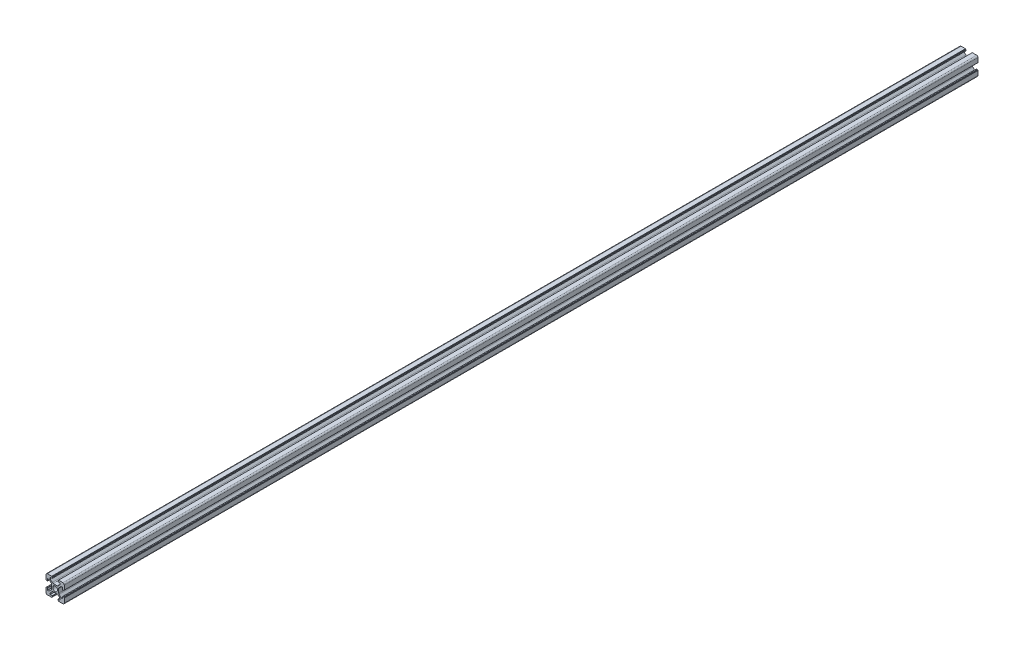
SolidWorks part; units mm, degrees
material "6063 T5"
ref_plane "Спереди" through (0, 0, 0) normal (0, 0, 1) x (1, 0, 0)
ref_plane "Сверху" through (0, 0, 0) normal (0, 1, 0) x (1, 0, 0)
ref_plane "Справа" through (0, 0, 0) normal (1, 0, 0) x (0, 0, -1)
sketch "Эскиз3" plane through (0, 0, 0) normal (0, 0, 1) x (1, 0, 0)
  line L0 (-10, 5.5) -> (-10, 8.5)
  line L5 (-8.5, 10) -> (-5.5, 10)
  line L7 (-9.9529, 9.1691) -> (10.0471, 9.1691) construction
  line L8 (5.5, 10) -> (8.5, 10)
  line L9 (10, 8.5) -> (10, 5.5)
  line L10 (10, -5.5) -> (10, -8.5)
  line L11 (8.5, -10) -> (5.5, -10)
  line L12 (-5.5, -10) -> (-8.5, -10)
  line L19 (-10, -8.5) -> (-10, -5.5)
  circle A0 centre (0, 0) radius 2.6
  arc A1 (-8.5, -10) -> (-10, -8.5) centre (-8.5, -8.5) cw
  arc A2 (10, -8.5) -> (8.5, -10) centre (8.5, -8.5) cw
  arc A3 (8.5, 10) -> (10, 8.5) centre (8.5, 8.5) cw
  arc A4 (-10, 8.5) -> (-8.5, 10) centre (-8.5, 8.5) cw
  point P0 (0, 0)
  point P4 (0, 0)
  point P30 (0, 0)
  line B0 (-8.2, 5.5) -> (-6.6, 5.5)
  line B1 (-6.6, 5.5) -> (-4.3393, 3.2393)
  line B2 (-3.9, 2.1787) -> (-3.9, -2.1787)
  line B3 (-4.3393, -3.2393) -> (-6.6, -5.5)
  line B4 (-6.6, -5.5) -> (-8.2, -5.5)
  line B5 (-8.2, -5.5) -> (-8.2, -3.25)
  line B6 (-8.35, -3.1) -> (-9.35, -3.1)
  line B7 (-9.5, -3.25) -> (-9.5, -3.45)
  line B8 (-9.65, -3.6) -> (-9.85, -3.6)
  line B9 (-9.85, 3.6) -> (-9.65, 3.6)
  line B10 (-9.5, 3.45) -> (-9.5, 3.25)
  line B11 (-9.35, 3.1) -> (-8.35, 3.1)
  line B12 (-8.2, 3.25) -> (-8.2, 5.5)
  line B13 (-10, 3.75) -> (-10, 5.5)
  line B14 (-10, -3.75) -> (-10, -5.5)
  line B15 (-10, 5.5) -> (-10, -5.5) construction
  arc B16 (-8.2, -3.25) -> (-8.35, -3.1) centre (-8.35, -3.25) ccw
  arc B17 (-9.35, -3.1) -> (-9.5, -3.25) centre (-9.35, -3.25) ccw
  arc B18 (-9.5, -3.45) -> (-9.65, -3.6) centre (-9.65, -3.45) cw
  arc B19 (-9.85, -3.6) -> (-10, -3.75) centre (-9.85, -3.75) ccw
  arc B20 (-8.35, 3.1) -> (-8.2, 3.25) centre (-8.35, 3.25) ccw
  arc B21 (-9.5, 3.25) -> (-9.35, 3.1) centre (-9.35, 3.25) ccw
  arc B22 (-9.65, 3.6) -> (-9.5, 3.45) centre (-9.65, 3.45) cw
  arc B23 (-10, 3.75) -> (-9.85, 3.6) centre (-9.85, 3.75) ccw
  arc B24 (-3.9, -2.1787) -> (-4.3393, -3.2393) centre (-5.4, -2.1787) cw
  arc B25 (-4.3393, 3.2393) -> (-3.9, 2.1787) centre (-5.4, 2.1787) cw
  line B26 (5.5, 8.2) -> (5.5, 6.6)
  line B27 (5.5, 6.6) -> (3.2393, 4.3393)
  line B28 (2.1787, 3.9) -> (-2.1787, 3.9)
  line B29 (-3.2393, 4.3393) -> (-5.5, 6.6)
  line B30 (-5.5, 6.6) -> (-5.5, 8.2)
  line B31 (-5.5, 8.2) -> (-3.25, 8.2)
  line B32 (-3.1, 8.35) -> (-3.1, 9.35)
  line B33 (-3.25, 9.5) -> (-3.45, 9.5)
  line B34 (-3.6, 9.65) -> (-3.6, 9.85)
  line B35 (3.6, 9.85) -> (3.6, 9.65)
  line B36 (3.45, 9.5) -> (3.25, 9.5)
  line B37 (3.1, 9.35) -> (3.1, 8.35)
  line B38 (3.25, 8.2) -> (5.5, 8.2)
  line B39 (3.75, 10) -> (5.5, 10)
  line B40 (-3.75, 10) -> (-5.5, 10)
  line B41 (5.5, 10) -> (-5.5, 10) construction
  arc B42 (-3.25, 8.2) -> (-3.1, 8.35) centre (-3.25, 8.35) ccw
  arc B43 (-3.1, 9.35) -> (-3.25, 9.5) centre (-3.25, 9.35) ccw
  arc B44 (-3.45, 9.5) -> (-3.6, 9.65) centre (-3.45, 9.65) cw
  arc B45 (-3.6, 9.85) -> (-3.75, 10) centre (-3.75, 9.85) ccw
  arc B46 (3.1, 8.35) -> (3.25, 8.2) centre (3.25, 8.35) ccw
  arc B47 (3.25, 9.5) -> (3.1, 9.35) centre (3.25, 9.35) ccw
  arc B48 (3.6, 9.65) -> (3.45, 9.5) centre (3.45, 9.65) cw
  arc B49 (3.75, 10) -> (3.6, 9.85) centre (3.75, 9.85) ccw
  arc B50 (-2.1787, 3.9) -> (-3.2393, 4.3393) centre (-2.1787, 5.4) cw
  arc B51 (3.2393, 4.3393) -> (2.1787, 3.9) centre (2.1787, 5.4) cw
  line B52 (8.2, -5.5) -> (6.6, -5.5)
  line B53 (6.6, -5.5) -> (4.3393, -3.2393)
  line B54 (3.9, -2.1787) -> (3.9, 2.1787)
  line B55 (4.3393, 3.2393) -> (6.6, 5.5)
  line B56 (6.6, 5.5) -> (8.2, 5.5)
  line B57 (8.2, 5.5) -> (8.2, 3.25)
  line B58 (8.35, 3.1) -> (9.35, 3.1)
  line B59 (9.5, 3.25) -> (9.5, 3.45)
  line B60 (9.65, 3.6) -> (9.85, 3.6)
  line B61 (9.85, -3.6) -> (9.65, -3.6)
  line B62 (9.5, -3.45) -> (9.5, -3.25)
  line B63 (9.35, -3.1) -> (8.35, -3.1)
  line B64 (8.2, -3.25) -> (8.2, -5.5)
  line B65 (10, -3.75) -> (10, -5.5)
  line B66 (10, 3.75) -> (10, 5.5)
  line B67 (10, -5.5) -> (10, 5.5) construction
  arc B68 (8.2, 3.25) -> (8.35, 3.1) centre (8.35, 3.25) ccw
  arc B69 (9.35, 3.1) -> (9.5, 3.25) centre (9.35, 3.25) ccw
  arc B70 (9.5, 3.45) -> (9.65, 3.6) centre (9.65, 3.45) cw
  arc B71 (9.85, 3.6) -> (10, 3.75) centre (9.85, 3.75) ccw
  arc B72 (8.35, -3.1) -> (8.2, -3.25) centre (8.35, -3.25) ccw
  arc B73 (9.5, -3.25) -> (9.35, -3.1) centre (9.35, -3.25) ccw
  arc B74 (9.65, -3.6) -> (9.5, -3.45) centre (9.65, -3.45) cw
  arc B75 (10, -3.75) -> (9.85, -3.6) centre (9.85, -3.75) ccw
  arc B76 (3.9, 2.1787) -> (4.3393, 3.2393) centre (5.4, 2.1787) cw
  arc B77 (4.3393, -3.2393) -> (3.9, -2.1787) centre (5.4, -2.1787) cw
  line B78 (-5.5, -8.2) -> (-5.5, -6.6)
  line B79 (-5.5, -6.6) -> (-3.2393, -4.3393)
  line B80 (-2.1787, -3.9) -> (2.1787, -3.9)
  line B81 (3.2393, -4.3393) -> (5.5, -6.6)
  line B82 (5.5, -6.6) -> (5.5, -8.2)
  line B83 (5.5, -8.2) -> (3.25, -8.2)
  line B84 (3.1, -8.35) -> (3.1, -9.35)
  line B85 (3.25, -9.5) -> (3.45, -9.5)
  line B86 (3.6, -9.65) -> (3.6, -9.85)
  line B87 (-3.6, -9.85) -> (-3.6, -9.65)
  line B88 (-3.45, -9.5) -> (-3.25, -9.5)
  line B89 (-3.1, -9.35) -> (-3.1, -8.35)
  line B90 (-3.25, -8.2) -> (-5.5, -8.2)
  line B91 (-3.75, -10) -> (-5.5, -10)
  line B92 (3.75, -10) -> (5.5, -10)
  line B93 (-5.5, -10) -> (5.5, -10) construction
  arc B94 (3.25, -8.2) -> (3.1, -8.35) centre (3.25, -8.35) ccw
  arc B95 (3.1, -9.35) -> (3.25, -9.5) centre (3.25, -9.35) ccw
  arc B96 (3.45, -9.5) -> (3.6, -9.65) centre (3.45, -9.65) cw
  arc B97 (3.6, -9.85) -> (3.75, -10) centre (3.75, -9.85) ccw
  arc B98 (-3.1, -8.35) -> (-3.25, -8.2) centre (-3.25, -8.35) ccw
  arc B99 (-3.25, -9.5) -> (-3.1, -9.35) centre (-3.25, -9.35) ccw
  arc B100 (-3.6, -9.65) -> (-3.45, -9.5) centre (-3.45, -9.65) cw
  arc B101 (-3.75, -10) -> (-3.6, -9.85) centre (-3.75, -9.85) ccw
  arc B102 (2.1787, -3.9) -> (3.2393, -4.3393) centre (2.1787, -5.4) cw
  arc B103 (-3.2393, -4.3393) -> (-2.1787, -3.9) centre (-2.1787, -5.4) cw
  dimension "D3" = 5.2
  dimension "D5" = 1.5
  dimension "D1" = 10
  dimension "D2" = 4
  dimension "D4" = 20
sketch_block_instance "6B-1"
sketch_block "Блок2" parameters "D5"=0.15, "D6"=1.5, "D1"=11, "D2"=1.6, "D3"=135, "D4"=7.2
sketch_block_instance "Блок2-2"
sketch_block_instance "Блок2-3"
sketch_block_instance "Блок2-4"
extrude "Бобышка-Вытянуть1" add sketch "Эскиз3" along normal blind 1000 contours L7 A4 L0 B13 B23 B9 B22 B10 B21 B11 B20 B12 B0 B1 B25 B2 B24 B3 B4 B5 B16 B6 B17 B7 B18 B8 B19 B14 L19 A1 L12 B91 B101 B87 B100 B88 B99 B89 B98 B90 B78 B79 B103 B80 B102 B81 B82 B83 B94 B84 B95 | A4 L7 B32 B43 B33 B44 B34 B45 B40 L5 | B37 L7 A3 L8 B39 B49 B35 B48 B36 B47
